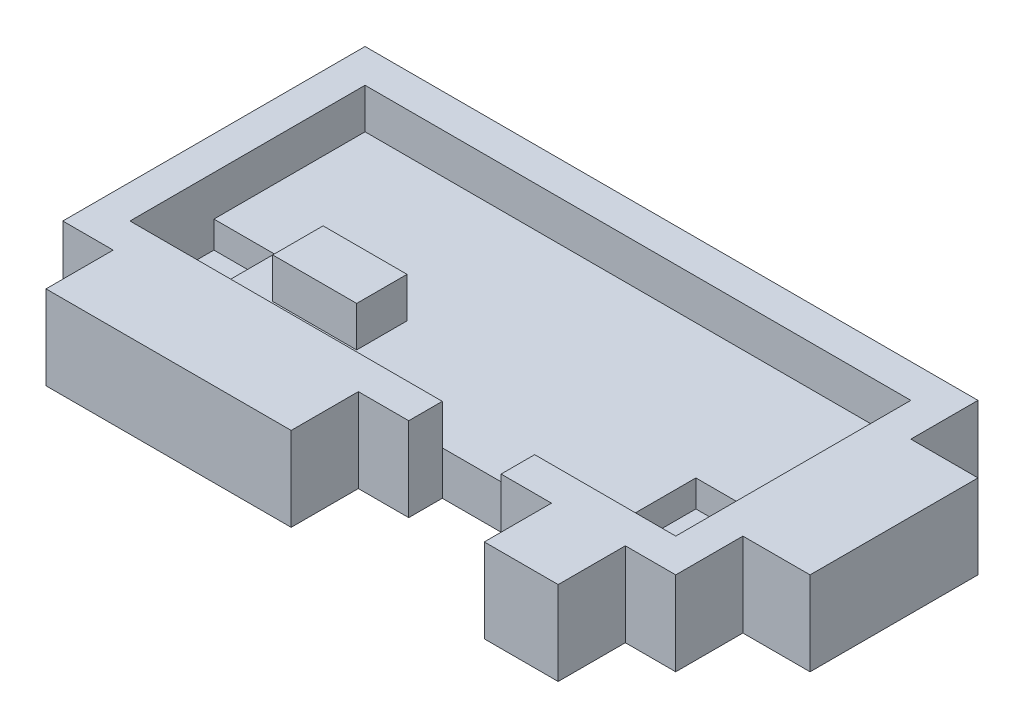
SolidWorks part; units mm, degrees
ref_plane "Front Plane" through (0, 0, 0) normal (0, 0, 1) x (1, 0, 0)
ref_plane "Top Plane" through (0, 0, 0) normal (0, 1, 0) x (1, 0, 0)
ref_plane "Right Plane" through (0, 0, 0) normal (1, 0, 0) x (0, 0, -1)
sketch "Sketch1" plane through (0, 0, 0) normal (0, 1, 0) x (1, 0, 0)
  line L1 (0, 0) -> (36.5, 0)
  line L2 (0, 0) -> (0, 18)
  line L3 (0, 18) -> (36.5, 18)
  line L4 (36.5, 0) -> (36.5, 18)
  dimension "D1" = 36.5
  dimension "D2" = 18
extrude "Boss-Extrude1" add sketch "Sketch1" against normal blind 5
sketch "Sketch2" plane through (0, 0, 0) normal (0, 1, 0) x (1, 0, 0)
  line L0 (36.5, 18) -> (0, 18) construction
  line L1 (2, 16) -> (34.5, 16)
  line L2 (2, 16) -> (2, 2)
  line L3 (2, 2) -> (34.5, 2)
  line L4 (34.5, 16) -> (34.5, 2)
  line L5 (0, 18) -> (0, 0) construction
  line L6 (0, 0) -> (36.5, 0) construction
  line L7 (36.5, 0) -> (36.5, 18) construction
  dimension "D1" = 2
  dimension "D2" = 2
  dimension "D3" = 2
  dimension "D4" = 2
extrude "Cut-Extrude1" cut sketch "Sketch2" against normal blind 2.4
sketch "Sketch3" plane through (0, -2.4, 0) normal (0, 1, 0) x (1, 0, 0)
  line L0 (34.5, 16) -> (2, 16) construction
  line L1 (8, 7.5) -> (13, 7.5)
  line L2 (8, 7.5) -> (8, 4.5)
  line L3 (8, 4.5) -> (13, 4.5)
  line L4 (13, 7.5) -> (13, 4.5)
  line L5 (2, 16) -> (2, 2) construction
  dimension "D1" = 3
  dimension "D2" = 8.5
  dimension "D3" = 5
  dimension "D4" = 6
extrude "Boss-Extrude2" add sketch "Sketch3" along normal blind 2.4
sketch "Sketch4" plane through (0, 0, -2) normal (0, 0, -1) x (-1, 0, 0)
  line L0 (-36.5, 0) -> (0, 0) construction
  line L1 (-26.1, 0) -> (-20.6, 0)
  line L2 (-26.1, 0) -> (-26.1, -5)
  line L3 (-26.1, -5) -> (-20.6, -5)
  line L4 (-20.6, 0) -> (-20.6, -5)
  line L5 (-36.5, -5) -> (-36.5, 0) construction
  dimension "D1" = 10.4
  dimension "D2" = 5.5
  dimension "D3" = 5
extrude "Cut-Extrude2" cut sketch "Sketch4" against normal up to next
sketch "Sketch5" plane through (0, -2.4, 0) normal (0, 1, 0) x (1, 0, 0)
  line L0 (2, 16) -> (2, 2) construction
  line L1 (2, 7) -> (5.6, 7)
  line L2 (2, 7) -> (2, 2)
  line L3 (2, 2) -> (5.6, 2)
  line L4 (5.6, 7) -> (5.6, 2)
  line L5 (2, 2) -> (20.6, 2) construction
  line L7 (34.5, 2) -> (29.7, 2)
  line L8 (34.5, 2) -> (34.5, 8)
  line L9 (34.5, 8) -> (29.7, 8)
  line L10 (29.7, 2) -> (29.7, 8)
  dimension "D1" = 3.6
  dimension "D2" = 5
  dimension "D3" = 0
  dimension "D4" = 6
  dimension "D5" = 4.8
extrude "Cut-Extrude3" cut sketch "Sketch5" against normal blind 1.6
sketch "Sketch6" plane through (0, 0, 0) normal (0, 0, 1) x (1, 0, 0)
  line L0 (0, 0) -> (20.6, 0) construction
  line L1 (3, 0) -> (17.6, 0)
  line L2 (3, 0) -> (3, -5)
  line L3 (3, -5) -> (17.6, -5)
  line L4 (17.6, 0) -> (17.6, -5)
  line L5 (0, -5) -> (20.6, -5) construction
  line L6 (0, -5) -> (0, 0) construction
  line L7 (20.6, -5) -> (20.6, 0) construction
  line L8 (26.1, 0) -> (36.5, 0) construction
  line L9 (29.1, 0) -> (33.5, 0)
  line L10 (29.1, 0) -> (29.1, -5)
  line L11 (29.1, -5) -> (33.5, -5)
  line L12 (33.5, 0) -> (33.5, -5)
  line L13 (26.1, -5) -> (36.5, -5) construction
  line L14 (36.5, -5) -> (36.5, 0) construction
  line L15 (26.1, 0) -> (26.1, -5) construction
  dimension "D1" = 3
  dimension "D2" = 3
  dimension "D3" = 3
  dimension "D4" = 3
extrude "Boss-Extrude3" add sketch "Sketch6" along normal blind 4
sketch "Sketch7" plane through (36.5, 0, 0) normal (1, 0, 0) x (0, 0, -1)
  line L0 (0, 0) -> (18, 0) construction
  line L1 (4, 0) -> (14, 0)
  line L2 (4, 0) -> (4, -5)
  line L3 (4, -5) -> (14, -5)
  line L4 (14, 0) -> (14, -5)
  line L5 (0, -5) -> (18, -5) construction
  line L6 (0, -5) -> (0, 0) construction
  line L7 (18, -5) -> (18, 0) construction
  dimension "D1" = 4
  dimension "D2" = 4
extrude "Boss-Extrude4" add sketch "Sketch7" along normal blind 4
